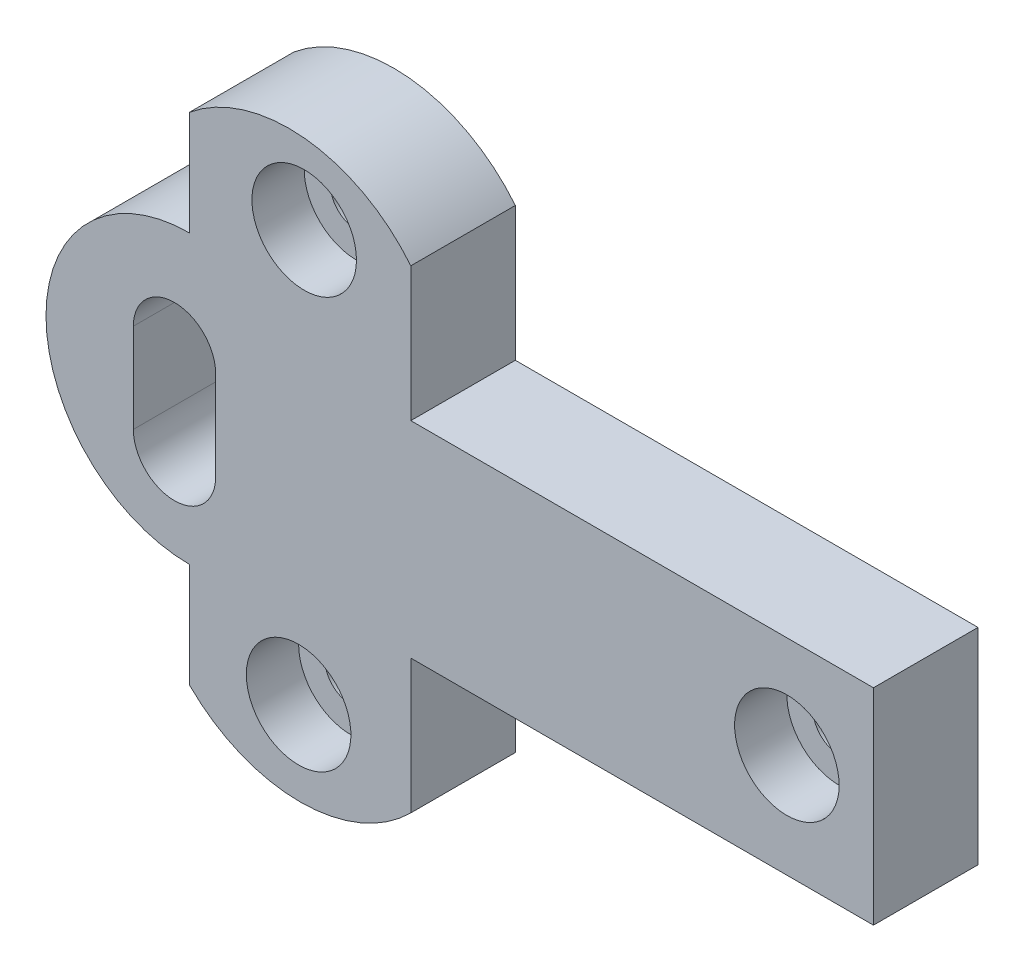
SolidWorks part; units mm, degrees
ref_plane "Front Plane" through (0, 0, 0) normal (0, 0, 1) x (1, 0, 0)
ref_plane "Top Plane" through (0, 0, 0) normal (0, 1, 0) x (1, 0, 0)
ref_plane "Right Plane" through (0, 0, 0) normal (1, 0, 0) x (0, 0, -1)
sketch "Sketch1" plane through (0, 0, 0) normal (0, 0, 1) x (1, 0, 0)
  line L0 (46.177, 17.5302) -> (-42.329, 17.5302)
  line L1 (-42.329, 17.5302) -> (-42.329, 43.1841)
  line L3 (-42.329, -47.4597) -> (-42.329, -21.8058)
  line L4 (-42.329, -21.8058) -> (46.177, -21.8058)
  line L5 (46.177, 17.5302) -> (46.177, -21.8058)
  line L8 (-84.6606, 47.4597) -> (-84.6606, 27.4597)
  line L9 (-84.6579, -47.4597) -> (-84.6579, -27.4597)
  arc A0 (-42.329, 43.1841) -> (-84.6606, 47.4597) centre (-65.6106, 24.3736) ccw
  arc A1 (-84.6579, -47.4597) -> (-42.329, -47.4597) centre (-63.4934, -26.2953) ccw
  arc A4 (-84.6579, -27.4597) -> (-84.6606, 27.4597) centre (-84.6593, 0) cw
  dimension "D1" = 20
  dimension "D2" = 20
extrude "Boss-Extrude1" add sketch "Sketch1" along normal blind 20
sketch "Sketch2" plane through (0, 0, 20) normal (0, 0, 1) x (1, 0, 0)
  line L0 (46.177, -2.1378) -> (-112.119, -0.0013) construction
  line L1 (46.177, -21.8058) -> (46.177, 17.5302) construction
  line L2 (-90.3402, 13.3085) -> (-90.3402, -13.8991) construction
  line L3 (-82.8402, 13.3085) -> (-82.8402, -13.8991)
  line L4 (-97.8402, 13.3085) -> (-97.8402, -13.8991)
  line L5 (-63.4934, -56.2264) -> (-62.6028, 54.1532) construction
  line L6 (-62.6028, 54.1532) -> (-62.7256, 38.9296)
  arc A0 (-84.6606, 27.4597) -> (-84.6579, -27.4597) centre (-84.6593, 0) ccw construction
  arc A1 (-82.8402, 13.3085) -> (-97.8402, 13.3085) centre (-90.3402, 13.3085) ccw
  arc A2 (-97.8402, -13.8991) -> (-82.8402, -13.8991) centre (-90.3402, -13.8991) ccw
  circle A3 centre (29.6123, -1.9143) radius 10
  circle A4 centre (29.6123, -1.9143) radius 9.759
  arc A5 (-84.6579, -47.4597) -> (-42.329, -47.4597) centre (-63.4934, -26.2953) ccw construction
  arc A6 (-42.329, 43.1841) -> (-84.6606, 47.4597) centre (-65.6106, 24.3736) ccw construction
  circle A7 centre (-62.7256, 38.9296) radius 10
  circle A8 centre (-62.7256, 38.9296) radius 10
  circle A9 centre (-63.7943, -40.2511) radius 10
  circle A10 centre (-63.7943, -40.2511) radius 10
  point P9 (-90.3402, -0.2953)
  dimension "D1" = 7.5
  dimension "D2" = 20
  dimension "D3" = 20
  dimension "D4" = 20
extrude "Cut-Extrude1" cut sketch "Sketch2" against normal blind 10 contours A7 | A3 | A9
sketch "Sketch3" plane through (0, 0, 20) normal (0, 0, 1) x (1, 0, 0)
  line L0 (29.6123, -1.9143) -> (-96.8183, -1.9143) construction
  line L1 (-87.5366, -10.4619) -> (-87.5366, 6.6334) construction
  line L2 (-95.412, -10.4619) -> (-95.412, 6.6334)
  line L3 (-79.6611, -10.4619) -> (-79.6611, 6.6334)
  arc A0 (-95.412, -10.4619) -> (-79.6611, -10.4619) centre (-87.5366, -10.4619) ccw
  arc A1 (-79.6611, 6.6334) -> (-95.412, 6.6334) centre (-87.5366, 6.6334) ccw
  point P5 (-87.5366, -1.9143)
extrude "Cut-Extrude2" cut sketch "Sketch3" against normal blind 20
sketch "Sketch4" plane through (0, 0, 20) normal (0, 0, 1) x (1, 0, 0)
  circle A0 centre (-62.7256, 38.9296) radius 5
  circle A1 centre (-63.7943, -40.2511) radius 5
  circle A2 centre (29.6123, -1.9143) radius 5
  dimension "D1" = 10
  dimension "D2" = 10
  dimension "D3" = 10
extrude "Cut-Extrude3" cut sketch "Sketch4" against normal blind 20
